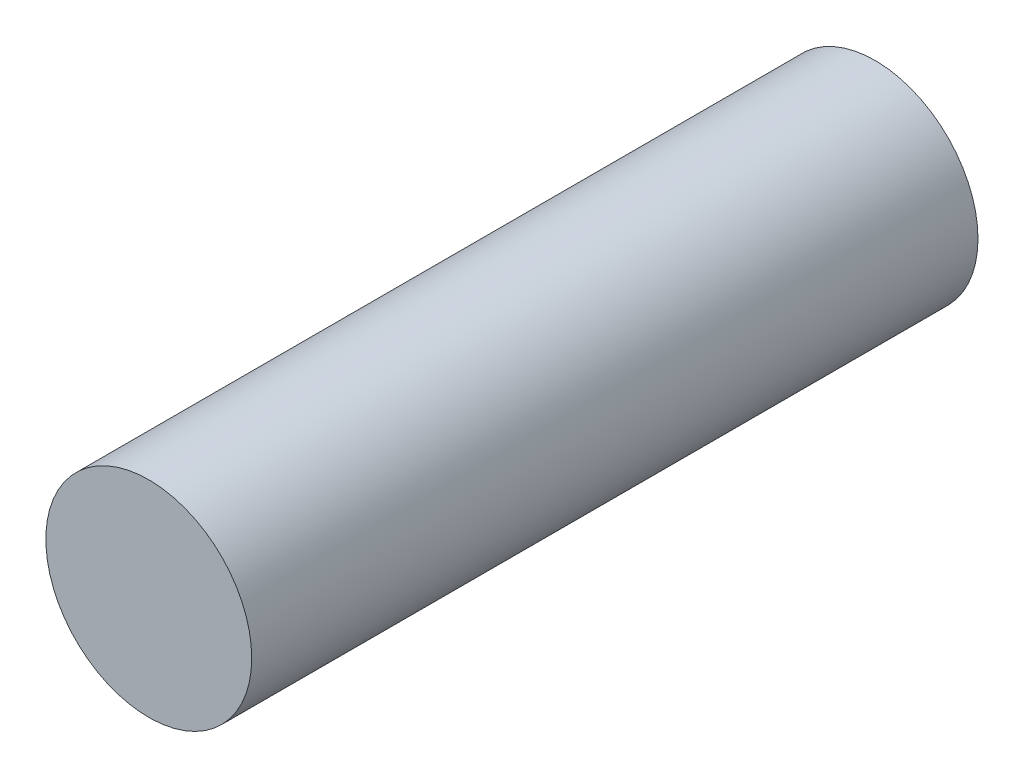
SolidWorks part; units mm, degrees
material "Alloy Steel"
ref_plane "Front" through (0, 0, 0) normal (0, 0, 1) x (1, 0, 0)
ref_plane "Top" through (0, 0, 0) normal (0, 1, 0) x (1, 0, 0)
ref_plane "Right" through (0, 0, 0) normal (1, 0, 0) x (0, 0, -1)
sketch "Sketch1" plane through (0, 0, 0) normal (0, 0, 1) x (1, 0, 0)
  circle A0 centre (0, 0) radius 7.135
  dimension "D1" = 14.27
extrude "Boss-Extrude1" add sketch "Sketch1" along normal blind 50.34
